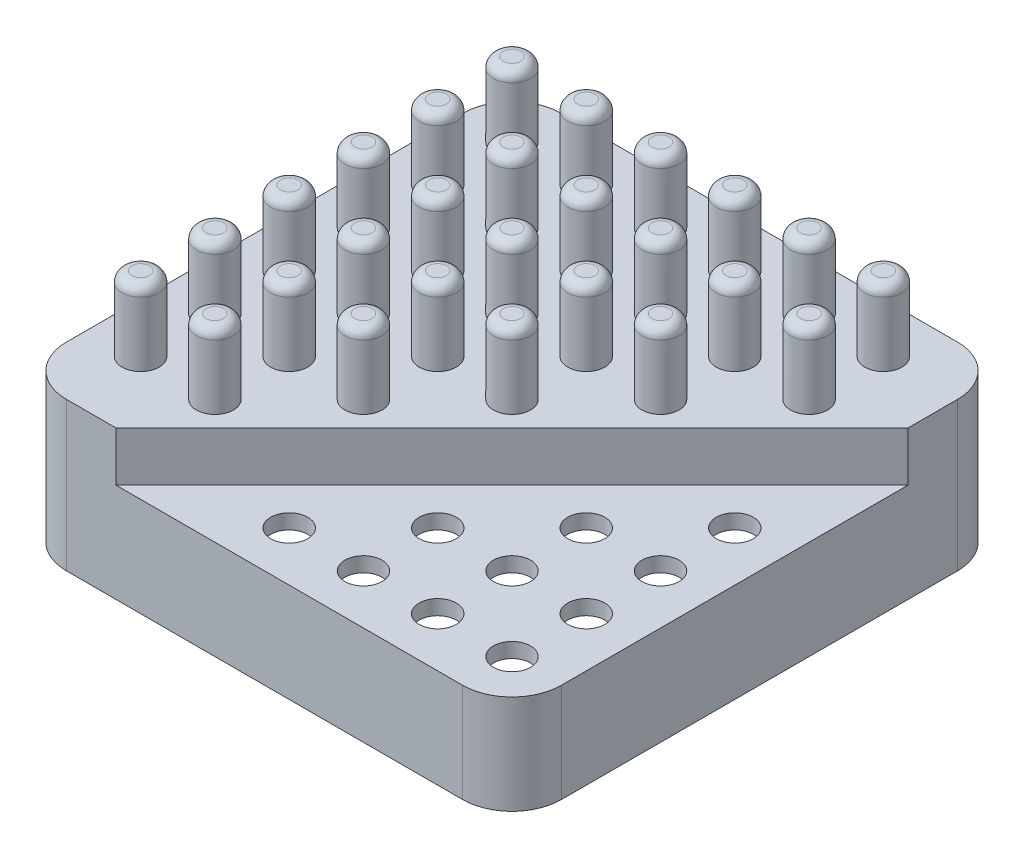
SolidWorks part; units mm, degrees
ref_plane "Front Plane" through (0, 0, 0) normal (0, 0, 1) x (1, 0, 0)
ref_plane "Top Plane" through (0, 0, 0) normal (0, 1, 0) x (1, 0, 0)
ref_plane "Right Plane" through (0, 0, 0) normal (1, 0, 0) x (0, 0, -1)
sketch "Sketch1" plane through (0, 0, 0) normal (0, 1, 0) x (1, 0, 0)
  line L1 (10, 0) -> (90, 0)
  line L2 (0, 10) -> (0, 90)
  line L3 (10, 100) -> (90, 100)
  line L4 (100, 10) -> (100, 90)
  arc A0 (10, 0) -> (0, 10) centre (10, 10) cw
  arc A1 (90, 0) -> (100, 10) centre (90, 10) ccw
  arc A2 (90, 100) -> (100, 90) centre (90, 90) cw
  arc A3 (0, 90) -> (10, 100) centre (10, 90) cw
  point P7 (0, 0)
  point P10 (100, 0)
  point P13 (100, 100)
  dimension "D3" = 10
  dimension "D1" = 100
  dimension "D2" = 100
extrude "Boss-Extrude1" add sketch "Sketch1" along normal blind 30
sketch "Sketch2" plane through (0, 30, 0) normal (0, 1, 0) x (1, 0, 0)
  line L0 (20, 0) -> (100, 80)
  line L1 (10, 0) -> (90, 0) construction
  line L2 (100, 10) -> (100, 90) construction
  line L3 (20, 0) -> (90, 0)
  line L4 (100, 10) -> (100, 80)
  arc A0 (90, 0) -> (100, 10) centre (90, 10) ccw construction
  arc A1 (90, 0) -> (100, 10) centre (90, 10) ccw
  dimension "D1" = 80
  dimension "D2" = 80
extrude "Cut-Extrude1" cut sketch "Sketch2" against normal blind 10
shell "Shell1" thickness 3
sketch "Sketch7" plane through (0, 20, 0) normal (0, 1, 0) x (1, 0, 0)
  circle A0 centre (90, 10) radius 3.75
  dimension "D1" = 7.5
extrude "Cut-Extrude2" cut sketch "Sketch7" against normal blind 10
pattern_linear "LPattern1" count 4 spacing 15 along (0, 0, -1) count 4 spacing 15 along (-1, 0, 0) skipping (1, 3), (2, 2), (2, 3), (3, 1), (3, 2), (3, 3) of "Cut-Extrude2"
sketch "Sketch8" plane through (0, 30, 0) normal (0, 1, 0) x (1, 0, 0)
  circle A0 centre (10, 90) radius 3.75
  dimension "D1" = 7.5
extrude "Boss-Extrude5" add sketch "Sketch8" along normal blind 15
fillet "Fillet1" radius 2 1 edges at (10, 45, -86.25)
pattern_linear "LPattern5" count 6 spacing 15 along (1, 0, 0) count 6 spacing 15 along (0, 0, 1) skipping (2, 5), (3, 4), (3, 5), (4, 3), (4, 4), (4, 5), (5, 2), (5, 3), (5, 4), (5, 5) of "Fillet1", "Boss-Extrude5"
